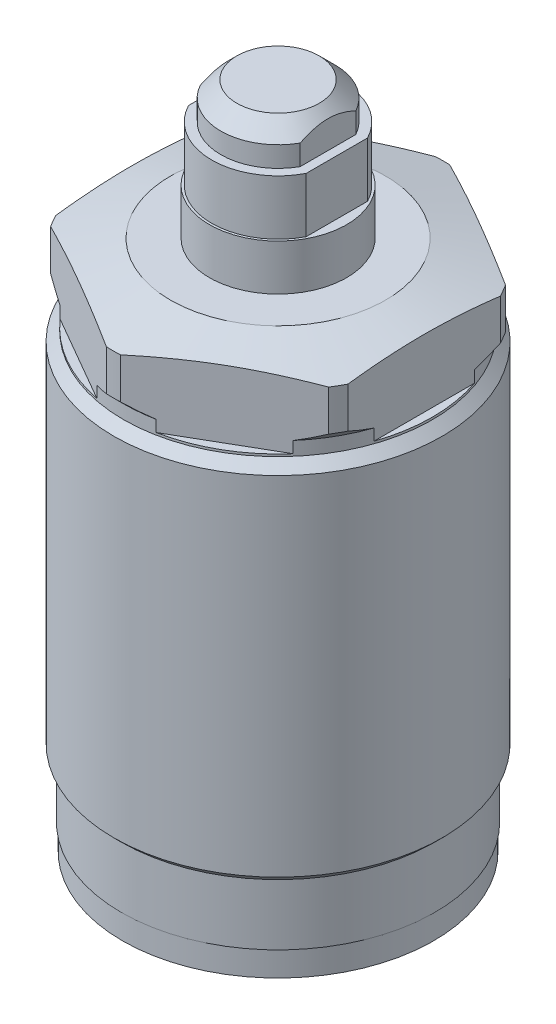
SolidWorks part; units mm, degrees
material "Alloy Steel"
ref_plane "Front Plane" through (0, 0, 0) normal (0, 0, 1) x (1, 0, 0)
ref_plane "Top Plane" through (0, 0, 0) normal (0, 1, 0) x (1, 0, 0)
ref_plane "Right Plane" through (0, 0, 0) normal (1, 0, 0) x (0, 0, -1)
sketch "Sketch1" plane through (0, 0, 0) normal (0, 0, 1) x (1, 0, 0)
  line L0 (0, 0) -> (0, -9.6761) construction
  line L1 (-17.125, 0) -> (-17, 0)
  line L2 (-17.125, 0) -> (-17.125, 6.65)
  line L3 (-17.125, 6.65) -> (-17.925, 7.45)
  line L4 (-17.925, 7.45) -> (-17.925, 45.45)
  line L5 (-17.925, 45.45) -> (-16.875, 46.5)
  line L6 (-16.875, 46.5) -> (-16.875, 48)
  line L7 (-16.875, 48) -> (-18, 49.125)
  line L8 (-18, 49.125) -> (-18, 53.5753)
  line L9 (-18, 53.5753) -> (-11.75, 55.25)
  line L10 (-11.75, 55.25) -> (0, 55.25)
  line L11 (0, 55.25) -> (0, -2.75)
  line L12 (-17, 0) -> (-17, -2.75)
  line L13 (-17, -2.75) -> (0, -2.75)
  dimension "D1" = 34.25
  dimension "D2" = 9.4
  dimension "D3" = 2.75
  dimension "D4" = 34
  dimension "D5" = 45
  dimension "D6" = 35.85
  dimension "D7" = 58
  dimension "D8" = 15
  dimension "D9" = 23.5
  dimension "D10" = 36
  dimension "D11" = 8.75
  dimension "D12" = 33.75
  dimension "D13" = 1.5
revolve "Revolve1" add sketch "Sketch1" angle 360 about L0
sketch "Sketch2" plane through (0, 55.25, 0) normal (0, 1, 0) x (1, 0, 0)
  line L1 (0, 18.429) -> (-15.96, 9.2145)
  line L2 (-15.96, 9.2145) -> (-15.96, -9.2145)
  line L3 (-15.96, -9.2145) -> (0, -18.429)
  line L4 (0, -18.429) -> (15.96, -9.2145)
  line L5 (15.96, -9.2145) -> (15.96, 9.2145)
  line L6 (15.96, 9.2145) -> (0, 18.429)
  circle A0 centre (0, 0) radius 15.96 construction
  dimension "D1" = 31.92
extrude "Cut-Extrude1" cut sketch "Sketch2" against normal blind 8.5 flip side to cut
sketch "Sketch4" plane through (0, 0, 0) normal (0, 0, 1) x (1, 0, 0)
  line L0 (0, 0) -> (0, 85.9979) construction
  line L1 (0, 70.25) -> (-6.25, 70.25)
  line L2 (-6.25, 70.25) -> (-6.25, 66.262)
  line L3 (-6.25, 66.262) -> (-7.25, 66.262)
  line L4 (-7.25, 66.262) -> (-7.25, 60.268)
  line L5 (-7.25, 60.268) -> (-7.5, 60.268)
  line L6 (-7.5, 60.268) -> (-7.5, 55.25)
  line L7 (11.75, 55.25) -> (-11.75, 55.25) construction
  line L8 (-7.5, 55.25) -> (0, 55.25)
  line L9 (0, 55.25) -> (0, 70.25)
  line L10 (-17, -2.75) -> (17, -2.75) construction
  dimension "D1" = 73
  dimension "D2" = 3.988
  dimension "D3" = 12.5
  dimension "D4" = 15
  dimension "D5" = 14.5
  dimension "D6" = 9.982
revolve "Revolve2" add sketch "Sketch4" angle 360 about L0
chamfer "Chamfer1" distance 1.754 angle 45 1 edges at (0, 70.25, -6.25)
sketch "Sketch5" plane through (0, 0, 0) normal (0, 0, 1) x (1, 0, 0)
  line L0 (7.25, 66.262) -> (-7.25, 66.262) construction
  line L1 (-5.46, 66.262) -> (-7.25, 66.262)
  line L2 (-5.46, 66.262) -> (-5.46, 70.25)
  line L3 (-5.46, 70.25) -> (-7.25, 70.25)
  line L4 (-7.25, 66.262) -> (-7.25, 70.25)
  line L5 (4.496, 70.25) -> (-4.496, 70.25) construction
  line L6 (-7.25, 66.262) -> (-7.25, 60.268) construction
  line L7 (0, 0) -> (0, 109.405) construction
  line L8 (7.25, 66.262) -> (7.25, 70.25)
  line L9 (5.46, 70.25) -> (7.25, 70.25)
  line L10 (5.46, 66.262) -> (5.46, 70.25)
  line L11 (5.46, 66.262) -> (7.25, 66.262)
  dimension "D1" = 10.92
extrude "Cut-Extrude2" cut sketch "Sketch5" against normal through all and the other way through all
sketch "Sketch6" plane through (0, 0, 0) normal (0, 0, 1) x (1, 0, 0)
  line L0 (7.25, 66.262) -> (-7.25, 66.262) construction
  line L1 (-6.425, 66.262) -> (-7.5, 66.262)
  line L2 (-6.425, 66.262) -> (-6.425, 60.268)
  line L3 (-6.425, 60.268) -> (-7.5, 60.268)
  line L4 (-7.5, 66.262) -> (-7.5, 60.268)
  line L5 (0, 0) -> (0, 83.5625) construction
  line L6 (7.5, 66.262) -> (7.5, 60.268)
  line L7 (6.425, 60.268) -> (7.5, 60.268)
  line L8 (6.425, 66.262) -> (6.425, 60.268)
  line L9 (6.425, 66.262) -> (7.5, 66.262)
  dimension "D1" = 12.85
extrude "Cut-Extrude3" cut sketch "Sketch6" against normal through all and the other way through all
